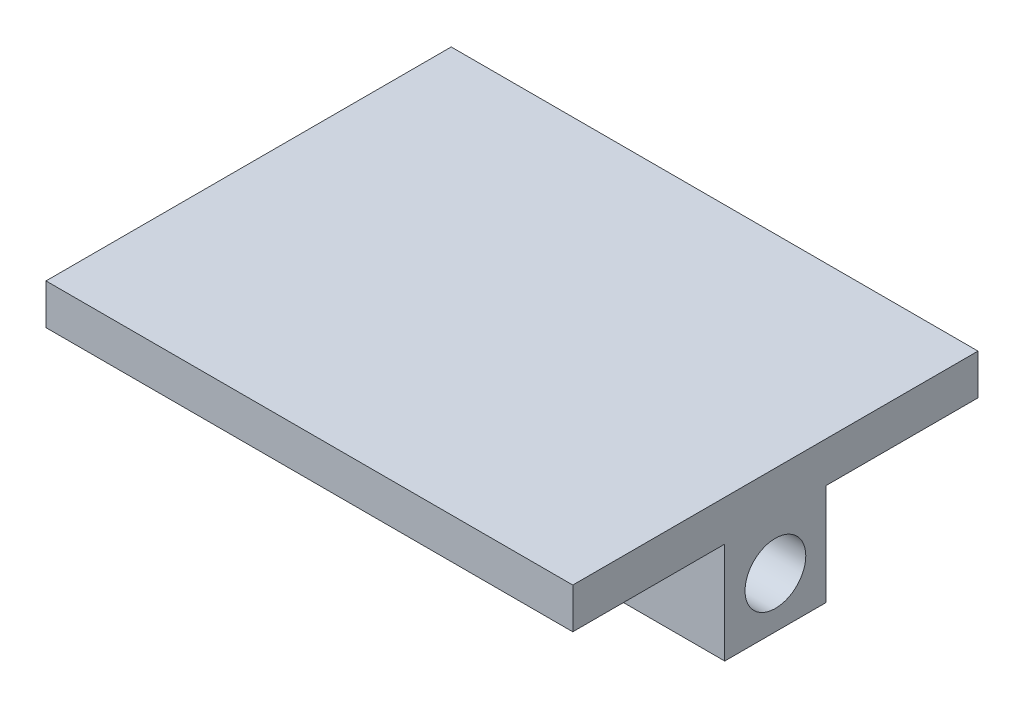
SolidWorks part; units mm, degrees
ref_plane "Front Plane" through (0, 0, 0) normal (0, 0, 1) x (1, 0, 0)
ref_plane "Top Plane" through (0, 0, 0) normal (0, 1, 0) x (1, 0, 0)
ref_plane "Right Plane" through (0, 0, 0) normal (1, 0, 0) x (0, 0, -1)
sketch "Sketch1" plane through (0, 0, 0) normal (0, 1, 0) x (1, 0, 0)
  line L1 (-82.55, 63.5) -> (82.55, 63.5)
  line L2 (-82.55, 63.5) -> (-82.55, -63.5)
  line L3 (-82.55, -63.5) -> (82.55, -63.5)
  line L4 (82.55, 63.5) -> (82.55, -63.5)
  line L5 (-82.55, 63.5) -> (82.55, -63.5) construction
  line L6 (-82.55, -63.5) -> (82.55, 63.5) construction
  point P0 (0, 0)
  dimension "D1" = 165.1
  dimension "D2" = 127
extrude "Boss-Extrude1" add sketch "Sketch1" along normal mid plane 12.7
sketch "Sketch2" plane through (0, -6.35, 0) normal (0, -1, 0) x (1, 0, 0)
  line L0 (82.55, 63.5) -> (82.55, -63.5) construction
  line L1 (-82.55, 15.875) -> (82.55, 15.875)
  line L2 (-82.55, 15.875) -> (-82.55, -15.875)
  line L3 (-82.55, -15.875) -> (82.55, -15.875)
  line L4 (82.55, 15.875) -> (82.55, -15.875)
  line L5 (-82.55, 15.875) -> (82.55, -15.875) construction
  line L6 (-82.55, -15.875) -> (82.55, 15.875) construction
  point P0 (0, 0)
  dimension "D1" = 31.75
extrude "Boss-Extrude2" add sketch "Sketch2" along normal blind 31.75
sketch "Sketch3" plane through (82.55, 0, 0) normal (1, 0, 0) x (0, 0, -1)
  line L0 (-15.875, -22.225) -> (15.875, -22.225) construction
  line L1 (-15.875, -38.1) -> (-15.875, -6.35) construction
  line L2 (15.875, -38.1) -> (15.875, -6.35) construction
  circle A0 centre (0, -22.225) radius 9.525
  dimension "D1" = 19.05
extrude "Cut-Extrude1" cut sketch "Sketch3" against normal up to next
sketch "Sketch4" plane through (0, 6.35, 0) normal (0, 1, 0) x (1, 0, 0)
  line L0 (-82.55, 0) -> (82.55, 0) construction
  line L1 (-82.55, 63.5) -> (-82.55, -63.5) construction
  line L2 (82.55, -63.5) -> (82.55, 63.5) construction
  line L3 (0, 63.5) -> (0, -63.5) construction
  line L4 (82.55, 63.5) -> (-82.55, 63.5) construction
  line L5 (-82.55, -63.5) -> (82.55, -63.5) construction
